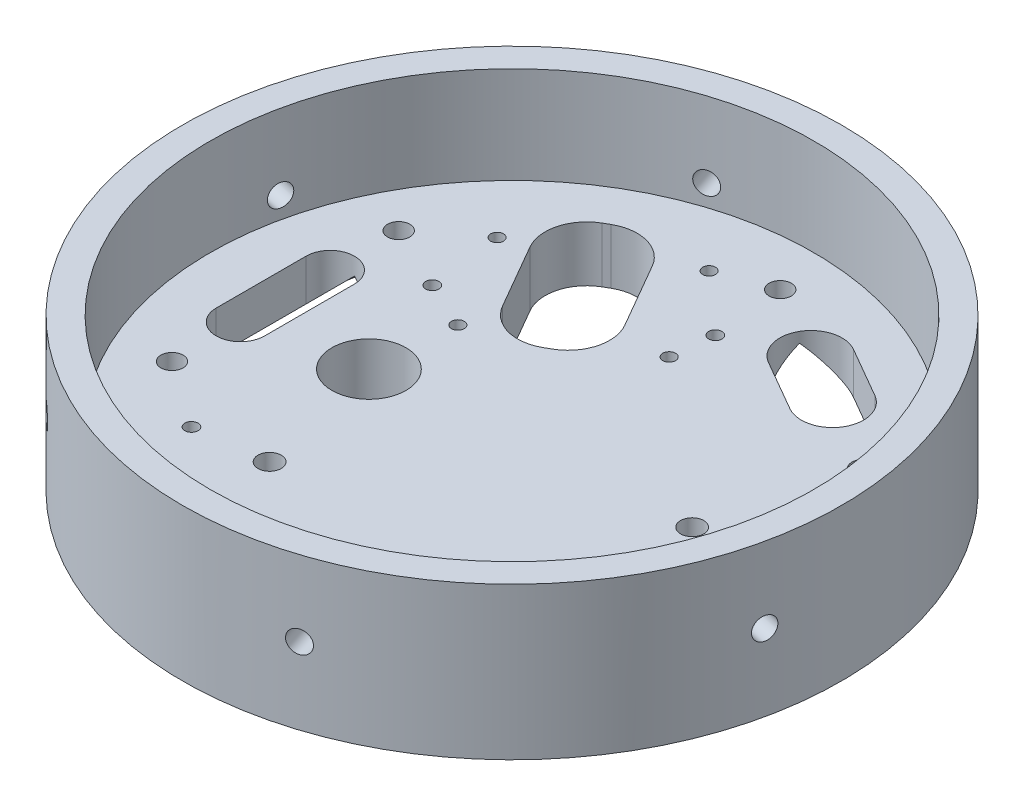
SolidWorks part; units mm, degrees
material "6061-T4 (SS)"
ref_plane "Front Plane" through (0, 0, 0) normal (0, 0, 1) x (1, 0, 0)
ref_plane "Top Plane" through (0, 0, 0) normal (0, 1, 0) x (1, 0, 0)
ref_plane "Right Plane" through (0, 0, 0) normal (1, 0, 0) x (0, 0, -1)
sketch "Sketch1" plane through (0, 0, 0) normal (0, 1, 0) x (1, 0, 0)
  circle A0 centre (0, 0) radius 75.692
  circle A1 centre (0, 0) radius 69.342
  dimension "D1" = 151.384
  dimension "D2" = 138.684
extrude "Boss-Extrude1" add sketch "Sketch1" along normal blind 22.225
sketch "Sketch2" plane through (0, 0, 0) normal (0, -1, 0) x (1, 0, 0)
  circle A0 centre (0, 0) radius 75.692
  dimension "D1" = 151.384
extrude "Boss-Extrude2" add sketch "Sketch2" along normal blind 12.7
hole_wizard "Tap Drill for 1/4-20 Tap1" positions "3DSketch2" profile "Sketch4" hole size "1/4-20" standard "ANSI Inch"
sketch3d "3DSketch2"
  line L0 (73.6526, 22.225, 17.4519) -> (73.9972, 4.8963, 15.9279)
  circle A1 centre (0, 22.225, 0) radius 75.692 construction
  point P0 (73.9972, 4.8963, 15.9279)
  point P10 (0, 97.917, 0)
  point P12 (-133.403, 50.4262, 0)
  dimension "D1" = 17.399
sketch "Sketch4" plane through (73.9972, 4.8963, 15.9279) normal (0, 1, 0) x (0.2104, 0, -0.9776)
  line L0 (0, 0) -> (0, 11.1858)
  line L1 (0, 11.1858) -> (2.5527, 9.652)
  line L2 (2.5527, 9.652) -> (2.5527, 0)
  line L5 (2.5527, 0) -> (0, 0)
  line L10 (0, 11.1858) -> (-2.5527, 9.652) construction
  line L11 (0, -6.35) -> (0, 107.95) construction
  dimension "Hole Dia." = 5.1054
  dimension "Hole Depth" = 9.652
  dimension "Drill Angle" = 118
pattern_circular "CirPattern1" count 6 over 360 about axis through (0, 22.225, 0) along (0, -1, 0) of "Tap Drill for 1/4-20 Tap1"
sketch "Sketch5" plane through (0, 0, 0) normal (0, 1, 0) x (1, 0, 0)
  line L0 (0, 0) -> (0, -69.342) construction
  line L1 (-52.6502, -15.6476) -> (-45.3536, -9.525)
  line L2 (-52.6502, -15.6476) -> (-19.9966, -54.5626)
  line L3 (-19.9966, -54.5626) -> (-12.7, -48.4401)
  line L4 (-45.3536, -9.525) -> (-12.7, -48.4401)
  circle A0 centre (0, 0) radius 69.342 construction
  dimension "D1" = 40
  dimension "D2" = 9.525
  dimension "D3" = 50.8
  dimension "D4" = 12.7
  dimension "D5" = 9.525
sketch "Sketch6" plane through (0, 0, 0) normal (0, 1, 0) x (1, 0, 0)
  line L0 (-52.07, -10.3188) -> (-52.07, 10.3187) construction
  line L1 (-57.6262, -10.3188) -> (-57.6262, 10.3188)
  line L2 (-46.5137, -10.3188) -> (-46.5137, 10.3188)
  line L3 (0, 0) -> (-103.2661, 0) construction
  line L4 (0, 0) -> (43.0826, 74.6212) construction
  line L5 (0, 0) -> (48.0262, -83.1838) construction
  line L6 (31.878, 41.7205) -> (20.192, 48.4674) construction
  line L7 (28.3061, 35.5338) -> (16.6202, 42.2807)
  line L8 (35.4498, 47.9072) -> (23.7639, 54.654)
  line L9 (50.1582, -15.7566) -> (40.6332, 0.7412) construction
  arc A0 (-57.6262, -10.3188) -> (-46.5137, -10.3188) centre (-52.07, -10.3188) ccw
  arc A1 (-46.5137, 10.3188) -> (-57.6262, 10.3188) centre (-52.07, 10.3187) ccw
  arc A2 (28.3061, 35.5338) -> (35.4498, 47.9072) centre (31.878, 41.7205) ccw
  arc A3 (23.7639, 54.654) -> (16.6202, 42.2807) centre (20.192, 48.4674) ccw
  circle A4 centre (40.6332, 0.7412) radius 2.667
  circle A5 centre (50.1582, -15.7566) radius 2.667
  point P2 (-52.07, 0)
  point P14 (26.035, 45.0939)
  dimension "D11" = 5.334
  dimension "D12" = 5.334
  dimension "D1" = 52.07
  dimension "D2" = 31.75
  dimension "D3" = 11.1125
  dimension "D4" = 120
  dimension "D5" = 120
  dimension "D6" = 14.2875
  dimension "D8" = 52.07
  dimension "D7" = 13.4937
  dimension "D9" = 35.56
  dimension "D10" = 19.05
  dimension "D13" = 40.64
extrude "Cut-Extrude1" cut sketch "Sketch6" against normal through all
chamfer "Chamfer1" distance 3.175 angle 45 8 edges at (29.6069, -12.7, -51.2806) (14.0054, -12.7, -52.0393) (38.0646, -12.7, -38.1486) (22.4631, -12.7, -38.9073) (-46.5137, -12.7, 0) (-52.07, -12.7, -15.875) (-52.07, -12.7, 15.875) (-57.6262, -12.7, 0)
sketch "Sketch7" plane through (0, 0, 0) normal (0, 0, 1) x (1, 0, 0)
  line L0 (-43.3387, -12.7) -> (-52.07, -3.9687)
  line L1 (-60.8013, -12.7) -> (-52.07, -3.9687)
  line L2 (-60.8013, -12.7) -> (-43.3387, -12.7)
extrude "Cut-Extrude2" cut sketch "Sketch7" against normal blind 22.225 and the other way blind 22.225
sketch "Sketch8" plane through (0, 0, 22.225) normal (0, 0, -1) x (-1, 0, 0)
  line L0 (52.07, -3.9687) -> (52.07, -12.7)
  line L1 (60.8013, -12.7) -> (43.3387, -12.7) construction
  line L2 (52.07, -12.7) -> (43.3387, -12.7)
  line L3 (43.3387, -12.7) -> (52.07, -3.9687)
revolve "Cut-Revolve1" cut sketch "Sketch8" angle 360 about L0
sketch "Sketch9" plane through (0, 0, -22.225) normal (0, 0, 1) x (1, 0, 0)
  line L0 (-52.07, -3.9687) -> (-52.07, -12.7)
  line L1 (-60.8013, -12.7) -> (-43.3387, -12.7) construction
  line L2 (-52.07, -12.7) -> (-60.8013, -12.7)
  line L3 (-60.8013, -12.7) -> (-52.07, -3.9687)
revolve "Cut-Revolve2" cut sketch "Sketch9" angle 360 about L0
sketch "Sketch10" plane through (0, -12.7, 0) normal (0, -1, 0) x (1, 0, 0)
  line L0 (41.7105, -27.7948) -> (3.2157, -50.0198) construction
  line L1 (28.3061, -35.5338) -> (16.6202, -42.2807) construction
  line L2 (41.7105, -27.7948) -> (45.2824, -33.9814) construction
  line L3 (45.2824, -33.9814) -> (6.7876, -56.2064)
  line L4 (6.7876, -56.2064) -> (3.2157, -50.0198) construction
  arc A0 (16.6202, -42.2807) -> (23.7639, -54.654) centre (20.192, -48.4674) ccw construction
  point P7 (22.4631, -38.9073)
  point P8 (22.4631, -38.9073)
  point P13 (14.0054, -52.0393)
  dimension "D1" = 44.45
sketch3d "3DSketch4"
  line L0 (20.8756, -12.7, -36.1576) -> (26.035, -2.3813, -45.0939)
  line L1 (15.0327, -12.7, -39.5311) -> (26.7186, -12.7, -32.7842) construction
  line L2 (31.1944, -12.7, -54.0302) -> (26.035, -2.3813, -45.0939)
  line L3 (37.0373, -12.7, -50.6568) -> (25.3514, -12.7, -57.4037) construction
  line L5 (31.1944, -12.7, -54.0302) -> (20.8756, -12.7, -36.1576)
  dimension "D1" = 90
sweep "Cut-Sweep1" cut profiles "3DSketch4" path "Sketch10"
sketch "Sketch11" plane through (-19.2474, 0, -11.1125) normal (0.866, 0, 0.5) x (0.5, 0, -0.866)
  line L0 (41.7512, -12.7) -> (52.07, -2.3813) construction
  line L1 (41.7512, -12.7) -> (52.07, -2.3813)
  line L2 (41.7512, -12.7) -> (52.07, -12.7)
  line L3 (62.3887, -12.7) -> (41.7512, -12.7) construction
  line L4 (52.07, -12.7) -> (52.07, -2.3813)
revolve "Cut-Revolve3" cut sketch "Sketch11" angle 360 about L4
sketch "Sketch12" plane through (19.2474, 0, 11.1125) normal (-0.866, 0, -0.5) x (-0.5, 0, 0.866)
  line L0 (-52.07, -2.3813) -> (-62.3887, -12.7) construction
  line L1 (-52.07, -2.3813) -> (-62.3887, -12.7)
  line L2 (-62.3887, -12.7) -> (-52.07, -12.7)
  line L3 (-62.3887, -12.7) -> (-41.7512, -12.7) construction
  line L4 (-52.07, -12.7) -> (-52.07, -2.3813)
revolve "Cut-Revolve4" cut sketch "Sketch12" angle 360 about L4
hole_wizard "1/4-20 Tapped Hole1" positions "Sketch20" profile "Sketch21" tap size "1/4-20" standard "ANSI Inch" end condition through all
sketch "Sketch20" plane through (0, 0, 0) normal (0, 1, 0) x (1, 0, 0)
  line L0 (-52.07, 26.035) -> (-52.07, -26.035) construction
  line L2 (-46.5137, -10.3188) -> (-46.5137, 10.3188) construction
  line L3 (22.4631, 38.9073) -> (45.0101, 25.8898) construction
  line L4 (16.6202, 42.2807) -> (28.3061, 35.5338) construction
  line L5 (45.0101, 25.8898) -> (48.582, 32.0764) construction
  line L6 (48.582, 32.0764) -> (3.488, 58.1114) construction
  point P1 (-52.07, 26.035)
  point P2 (-52.07, -26.035)
  point P5 (-52.07, 0)
  point P8 (-46.5137, 0)
  point P16 (48.582, 32.0764)
  point P18 (3.488, 58.1114)
  dimension "D1" = 52.07
  dimension "D2" = 52.07
  dimension "D3" = 26.035
sketch "Sketch21" plane through (-52.07, 0, -26.035) normal (1, 0, 0) x (0, 0, 1)
  line L0 (0, 0) -> (0, 12.7)
  line L1 (0, 12.7) -> (2.5527, 12.7)
  line L2 (2.5527, 12.7) -> (2.5527, 0)
  line L5 (2.5527, 0) -> (0, 0)
  line L11 (0, -6.35) -> (0, 107.95) construction
  dimension "Thru Tap Drill Dia." = 5.1054
  dimension "Thru Tap Drill Depth" = 12.7
cosmetic thread "Hole Thread1" parameters "D2"=6.35
cosmetic thread "Hole Thread2" parameters "D2"=6.35
cosmetic thread "Hole Thread3" parameters "D2"=6.35
cosmetic thread "Hole Thread4" parameters "D2"=6.35
sketch "Sketch22" plane through (0, 0, 0) normal (0, 1, 0) x (1, 0, 0)
  line L0 (40.6332, 0.7412) -> (50.1582, -15.7566) construction
  line L2 (-4.1721, -58.6755) -> (-12.1096, -44.9274) construction
  line L3 (-20.0471, -31.1792) -> (-4.1721, -58.6755) construction
  line L4 (-8.5715, -61.2155) -> (-16.509, -47.4674) construction
  line L5 (-8.5715, -61.2155) -> (-24.4465, -33.7192) construction
  line L6 (-9.174, -50.0121) -> (-13.5734, -52.5521) construction
  line L7 (-12.1096, -44.9274) -> (-20.0471, -31.1792) construction
  line L8 (-20.0471, -31.1792) -> (-24.4465, -33.7192) construction
  line L9 (-24.4465, -33.7192) -> (-16.509, -47.4674) construction
  line L11 (-23.0984, -36.0543) -> (-18.699, -33.5143) construction
  circle A0 centre (-39.4004, 35.9616) radius 1.4732
  circle A1 centre (-26.496, 14.0643) radius 1.4732
  circle A2 centre (4.1249, 31.9744) radius 1.4732
  circle A3 centre (-8.4119, 53.6837) radius 1.4732
  circle A6 centre (-20.8987, -34.7843) radius 2.667
  circle A7 centre (-11.3737, -51.2821) radius 2.667
extrude "Cut-Extrude3" cut sketch "Sketch22" against normal blind 77.47
sketch "Sketch23" plane through (0, 0, 0) normal (0, 1, 0) x (1, 0, 0)
  line L0 (0, 0) -> (-120.9707, 0) construction
  line L1 (0, 0) -> (-47.0979, 81.5759) construction
  line L2 (-20.3388, 14.6538) -> (-2.5212, 24.9408)
  line L3 (-20.3388, 14.6538) -> (-38.4998, 46.1096)
  line L4 (-2.5212, 24.9408) -> (-20.6822, 56.3966)
  line L5 (-20.6822, 56.3966) -> (-38.4998, 46.1096)
  line L6 (0, 0) -> (-27.94, -4.9266) construction
  circle A0 centre (-8.4119, 53.6837) radius 1.4732
  circle A1 centre (4.1249, 31.9744) radius 1.4732
  circle A2 centre (-26.496, 14.0643) radius 1.4732
  circle A3 centre (-39.4004, 35.9616) radius 1.4732
  circle A4 centre (-27.94, -4.9266) radius 8.509
  dimension "D5" = 27.94
  dimension "D1" = 60
  dimension "D2" = 22.86
  dimension "D3" = 36.322
  dimension "D4" = 20.574
  dimension "D6" = 70
extrude "Cut-Extrude4" cut sketch "Sketch23" against normal up to next (12.7 mm away)
fillet "Fillet2" radius 9.525 4 edges at (-20.3388, -6.35, -14.6538) (-2.5212, -6.35, -24.9408) (-20.6822, -6.35, -56.3966) (-38.4998, -6.35, -46.1096)
hole_wizard "Tapped Hole for #4-40 Helicoil1" positions "Sketch24" profile "Sketch25" tap size "#4-40" standard "Helicoil® Inch" end condition up to next
sketch "Sketch24" plane through (0, -12.7, 0) normal (0, -1, 0) x (-1, 0, 0)
  point P0 (37.3421, 19.0267)
  point P3 (-5.1075, 41.5976)
  point P6 (-50.2958, 13.4767)
  point P9 (36.8191, -36.8191)
sketch "Sketch25" plane through (-37.3421, -12.7, -19.0267) normal (1, 0, 0) x (0, 0, -1)
  line L0 (0, 0) -> (0, 12.7)
  line L1 (0, 12.7) -> (1.524, 12.7)
  line L2 (1.524, 12.7) -> (1.524, 0)
  line L5 (1.524, 0) -> (0, 0)
  line L11 (0, -6.35) -> (0, 107.95) construction
  dimension "Thru Tap Drill Dia." = 3.048
  dimension "Thru Tap Drill Depth" = 12.7
cosmetic thread "Hole Thread5" parameters "D1"=3.556, "D2"=3.7414
cosmetic thread "Hole Thread6" parameters "D1"=3.556, "D2"=3.7414
cosmetic thread "Hole Thread7" parameters "D1"=3.556, "D2"=3.7414
cosmetic thread "Hole Thread8" parameters "D1"=3.556, "D2"=3.7414
equation "\"D7@Sketch6\"=(9/16)+0.25-(0.5*\"D6@Sketch6\")"
